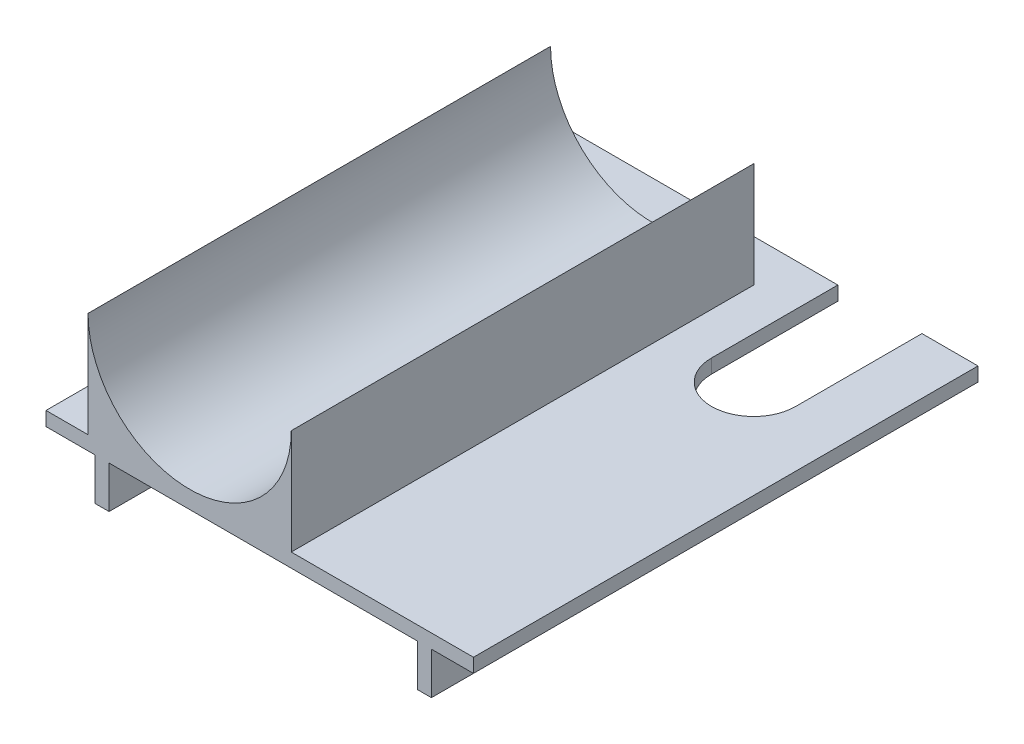
SolidWorks part; units mm, degrees
ref_plane "Front Plane" through (0, 0, 0) normal (0, 0, 1) x (1, 0, 0)
ref_plane "Top Plane" through (0, 0, 0) normal (0, 1, 0) x (1, 0, 0)
ref_plane "Right Plane" through (0, 0, 0) normal (1, 0, 0) x (0, 0, -1)
sketch "Sketch1" plane through (0, 0, 0) normal (0, 0, 1) x (1, 0, 0)
  line L0 (-121.5804, 5) -> (327.8331, 5) construction
  line L14 (-117.1153, 77.5) -> (146.5294, 77.5) construction
  line L15 (-72.5, 2.5) -> (-102.5, 2.5)
  line L16 (72.5, 2.5) -> (202.5, 2.5)
  line L17 (-102.5, 2.5) -> (-102.5, -7.5)
  line L18 (-102.5, -7.5) -> (-67.5, -7.5)
  line L19 (202.5, -7.5) -> (202.5, 2.5)
  line L20 (-67.5, -7.5) -> (-67.5, -37.5)
  line L21 (-67.5, -37.5) -> (-57.5, -37.5)
  line L22 (-57.5, -37.5) -> (-57.5, -7.5)
  line L25 (-57.5, -7.5) -> (57.5, -7.5)
  line L26 (0, 116.8813) -> (0, -101.7468) construction
  line L30 (67.5, -7.5) -> (162.5, -7.5)
  line L31 (57.5, -7.5) -> (67.5, -7.5)
  line L32 (162.5, -7.5) -> (162.5, -37.5)
  line L33 (162.5, -37.5) -> (172.5, -37.5)
  line L34 (172.5, -37.5) -> (172.5, -7.5)
  line L35 (172.5, -7.5) -> (202.5, -7.5)
  line L36 (-72.5, 77.5) -> (-72.5, 2.5)
  line L37 (72.5, 77.5) -> (72.5, 2.5)
  arc A2 (-72.5, 77.5) -> (72.5, 77.5) centre (0, 77.5) ccw
  dimension "D1" = 145
  dimension "D11" = 35
  dimension "D10" = 2.5
  dimension "D2" = 10
  dimension "D3" = 2.5
  dimension "D4" = 10
  dimension "D5" = 30
  dimension "D6" = 10
  dimension "D7" = 30
  dimension "D8" = 10
  dimension "D9" = 30
extrude "Boss-Extrude1" add sketch "Sketch1" against normal blind 360
sketch "Sketch3" plane through (0, 2.5, 0) normal (0, 1, 0) x (1, 0, 0)
  line L0 (102.5, 360) -> (102.5, 270)
  line L1 (202.5, 360) -> (72.5, 360) construction
  line L3 (162.5, 270) -> (162.5, 360)
  line L4 (102.5, 360) -> (162.5, 360)
  line L5 (202.5, 360) -> (202.5, 0) construction
  line L7 (130, 240) -> (130, 230.6325) construction
  arc A2 (102.5, 270) -> (162.5, 270) centre (132.5, 269.8958) ccw
  dimension "D4" = 30.0002
  dimension "D1" = 60
  dimension "D2" = 40
  dimension "D3" = 90
extrude "Cut-Extrude1" cut sketch "Sketch3" against normal blind 360
sketch "Sketch4" plane through (-72.5, 0, 0) normal (-1, 0, 0) x (0, 0, 1)
  line L0 (-360, 2.5) -> (0, 2.5) construction
  line L1 (-360, 77.5) -> (-330, 77.5)
  line L2 (-360, 77.5) -> (-360, 2.5)
  line L3 (-360, 2.5) -> (-330, 2.5)
  line L4 (-330, 77.5) -> (-330, 2.5)
  line L6 (-360, 77.5) -> (0, 77.5)
  line L7 (-360, 77.5) -> (-360, -37.5)
  line L8 (-360, -37.5) -> (0, -37.5)
  line L9 (0, 77.5) -> (0, -37.5)
  line M4 (0, 77.5) -> (-360, 77.5)
  line M5 (-360, 77.5) -> (-360, 2.5)
  line M6 (-360, 2.5) -> (0, 2.5)
  dimension "D1" = 30
extrude "Cut-Extrude2" cut sketch "Sketch4" against normal through all contours L4 M4 M5 M6
